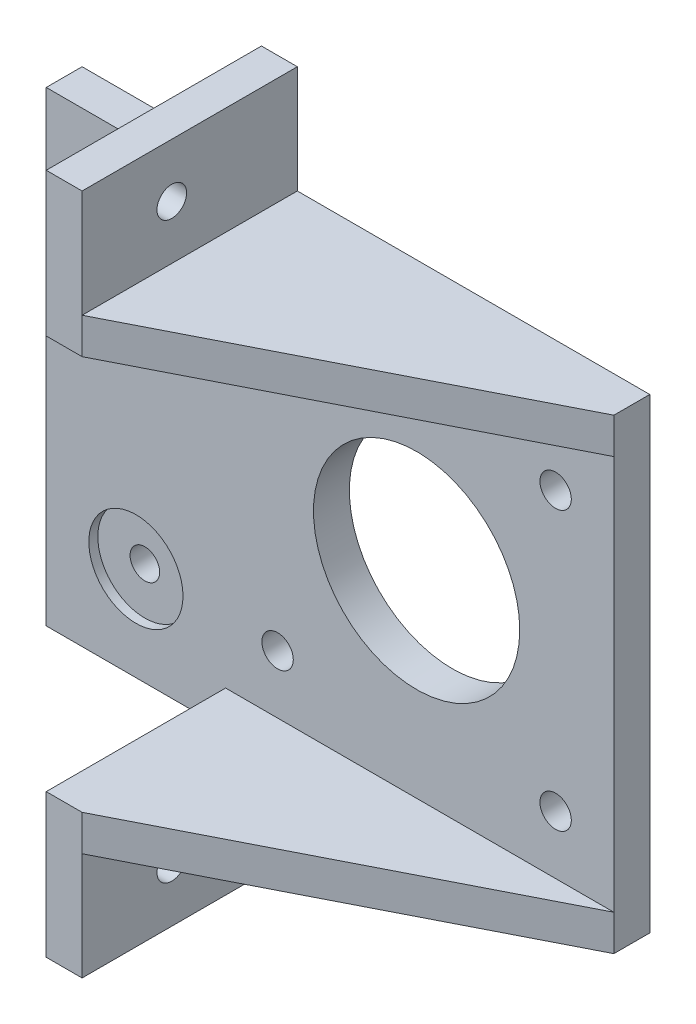
SolidWorks part; units mm, degrees
ref_plane "Plano frontal" through (0, 0, 0) normal (0, 0, 1) x (1, 0, 0)
ref_plane "Plano superior" through (0, 0, 0) normal (0, 1, 0) x (1, 0, 0)
ref_plane "Plano direito" through (0, 0, 0) normal (1, 0, 0) x (0, 0, -1)
sketch "Esboço1" plane through (0, 0, 0) normal (0, 0, 1) x (1, 0, 0)
  line L0 (-41.3, 0) -> (-25.3872, 0) construction
  line L1 (-15.5, 15.5) -> (15.5, 15.5) construction
  line L2 (-15.5, 15.5) -> (-15.5, -15.5) construction
  line L3 (-15.5, -15.5) -> (15.5, -15.5) construction
  line L4 (15.5, 15.5) -> (15.5, -15.5) construction
  line L5 (-15.5, 15.5) -> (15.5, -15.5) construction
  line L6 (-15.5, -15.5) -> (15.5, 15.5) construction
  line L7 (22, 26) -> (-41.3, 26)
  line L8 (22, 26) -> (22, -26)
  line L9 (22, -26) -> (-41.3, -26)
  line L10 (-41.3, 26) -> (-41.3, -26)
  line L11 (-21.3, -26) -> (-21.3, 26) construction
  circle A0 centre (0, 0) radius 11.5
  circle A1 centre (-15.5, 15.5) radius 1.75
  circle A2 centre (15.5, 15.5) radius 1.75
  circle A3 centre (15.5, -15.5) radius 1.75
  circle A4 centre (-15.5, -15.5) radius 1.75
  circle A5 centre (-31.3, -15.5) radius 1.65
  circle A6 centre (-31.3, 15.5) radius 1.65
  point P16 (22, 0)
  dimension "D1" = 3.5
  dimension "D2" = 23
  dimension "D7" = 3.3
  dimension "D3" = 31
  dimension "D4" = 52
  dimension "D5" = 22
  dimension "D6" = 21.3
  dimension "D8" = 20
  dimension "D9" = 10
  dimension "D10" = 31
extrude "Ressalto-extrusão1" add sketch "Esboço1" along normal blind 25
sketch "Esboço2" plane through (0, 0, 0) normal (0, 1, 0) x (1, 0, 0)
  line L0 (22, -4) -> (-23, -4)
  line L1 (22, -25) -> (22, 0) construction
  line L2 (-28, -4) -> (-28, -25)
  line L3 (22, -25) -> (-41.3, -25) construction
  line L4 (-23, -25) -> (22, -4)
  line L5 (-41.3, -4) -> (-23, -4)
  line L6 (-41.3, -25) -> (-41.3, 0) construction
  line L8 (22, 0) -> (-41.3, 0) construction
  line L9 (-41.3, -4) -> (-41.3, -25)
  line L10 (-41.3, -25) -> (-23, -25)
  line L11 (-23, -25) -> (22, -25)
  line L12 (22, -25) -> (22, -4)
  dimension "D1" = 4
  dimension "D2" = 45
  dimension "D3" = 5
extrude "Corte-extrusão1" cut sketch "Esboço2" against normal through all both and the other way through all
sketch "Esboço3" plane through (0, 26, 0) normal (0, 1, 0) x (1, 0, 0)
  line L0 (22, -4) -> (-17.3, -24)
  line L1 (-17.3, -24) -> (-21.3, -24)
  line L2 (-21.3, -24) -> (-21.3, -4)
  line L3 (-41.3, -4) -> (22, -4) construction
  line L4 (-21.3, -4) -> (22, -4)
  dimension "D1" = 20
  dimension "D2" = 4
  dimension "D3" = 20
extrude "Ressalto-extrusão2" add sketch "Esboço3" against normal blind 4
sketch "Esboço4" plane through (-21.3, 0, 0) normal (-1, 0, 0) x (0, 0, 1)
  line L0 (0, 26) -> (0, -26) construction
  line L1 (24, 22) -> (0, 22)
  line L2 (24, 22) -> (24, 38)
  line L3 (24, 38) -> (0, 38)
  line L4 (0, 22) -> (0, 38)
  line L5 (4, 26) -> (24, 26) construction
  circle A0 centre (14, 32) radius 1.65
  point P14 (14, 26)
  dimension "D3" = 3.3
  dimension "D1" = 16
  dimension "D2" = 6
extrude "Ressalto-extrusão3" add sketch "Esboço4" against normal blind 4 contours L3 L4 L1 L2
mirror "Espelhar1" about plane through (0, 0, 0) normal (0, 1, 0) of "Ressalto-extrusão3", "Ressalto-extrusão2"
sketch "Esboço5" plane through (-21.3, 0, 0) normal (-1, 0, 0) x (0, 0, 1)
  circle A0 centre (14, -32) radius 5.25
  circle A1 centre (14, 32) radius 5.25
  dimension "D1" = 10.5
  dimension "D2" = 10.5
extrude "Corte-extrusão2" cut sketch "Esboço5" against normal blind 1
sketch "Esboço6" plane through (0, 0, 4) normal (0, 0, 1) x (1, 0, 0)
  circle A0 centre (-31.3, 15.5) radius 5.25
  circle A1 centre (-31.3, -15.5) radius 5.25
  dimension "D1" = 10.5
extrude "Corte-extrusão3" cut sketch "Esboço6" against normal blind 1
